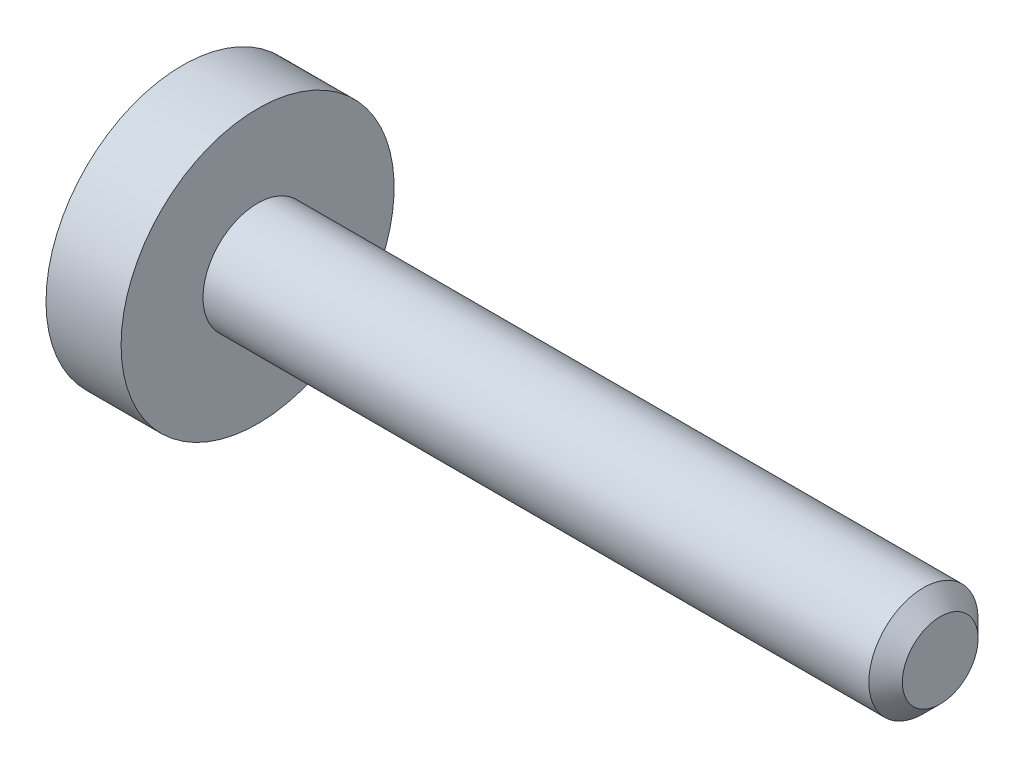
SolidWorks part; units mm, degrees
material "AISI 304"
ref_plane "正面" through (0, 0, 0) normal (0, 0, 1) x (1, 0, 0)
ref_plane "平面" through (0, 0, 0) normal (0, 1, 0) x (1, 0, 0)
ref_plane "右側面" through (0, 0, 0) normal (1, 0, 0) x (0, 0, -1)
ref_plane "Plane1" through (0, 0, 0) normal (0, 0, 1) x (1, 0, 0)
sketch "Sketch1" plane through (0, 0, 0) normal (0, 0, 1) x (1, 0, 0)
  line L0 (-1.1, 0) -> (-1.1, 2)
  line L1 (-1.1, 2) -> (0, 2)
  line L2 (0, 2) -> (0, 0.8)
  line L3 (0, 0.8) -> (9.7545, 0.8)
  line L4 (9.7545, 0.8) -> (10, 0.5545)
  line L5 (10, 0.5545) -> (10, 0)
  line L6 (10, 0) -> (-1.1, 0)
  line L7 (10, 0) -> (-1.1, 0) construction
  dimension "D1" = 0.8
revolve "Revolve1" add sketch "Sketch1" angle 360 about L7
cosmetic thread "Cosmetic Thread1"
ref_plane "Plane2" through (-1.1, 0, 0) normal (1, 0, 0) x (0, 0, -1)
sketch "Sketch2" plane through (-1.1, 0, 0) normal (1, 0, 0) x (0, 0, -1)
  line L0 (-0.65, -0.3753) -> (0, -0.7506)
  line L1 (0, -0.7506) -> (0.65, -0.3753)
  line L2 (0.65, -0.3753) -> (0.65, 0.3753)
  line L3 (0.65, 0.3753) -> (0, 0.7506)
  line L4 (0, 0.7506) -> (-0.65, 0.3753)
  line L5 (-0.65, 0.3753) -> (-0.65, -0.3753)
extrude "Cut-Extrude1" cut sketch "Sketch2" along normal blind 1.2
